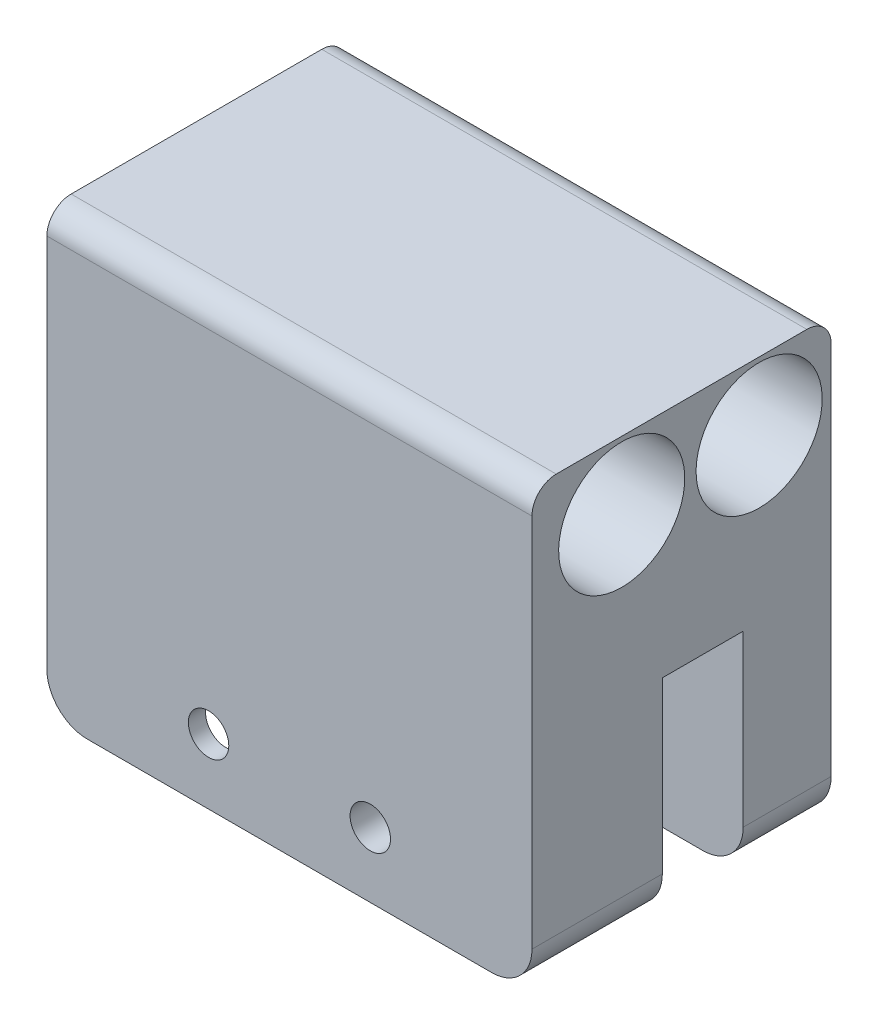
SolidWorks part; units mm, degrees
ref_plane "Front Plane" through (0, 0, 0) normal (0, 0, 1) x (1, 0, 0)
ref_plane "Top Plane" through (0, 0, 0) normal (0, 1, 0) x (1, 0, 0)
ref_plane "Right Plane" through (0, 0, 0) normal (1, 0, 0) x (0, 0, -1)
sketch "Esboço2" plane through (0, 0, 0) normal (0, 0, 1) x (1, 0, 0)
  line L7 (-246.2188, 113.8225) -> (-237.7812, 113.8225)
  line L8 (-201.9668, 113.8225) -> (-194.0332, 113.8225)
  line L9 (-250, 138.1236) -> (-250, 163.2122)
  line L10 (-245, 168.2122) -> (-195, 168.2122)
  line L11 (-190, 163.2122) -> (-190, 138.1236)
  line L21 (-194.0332, 113.8225) -> (-190, 113.8225)
  line L22 (-190, 113.8225) -> (-190, 138.1236)
  line L25 (-250, 138.1236) -> (-250, 113.8225)
  line L26 (-250, 113.8225) -> (-246.2188, 113.8225)
  line L27 (-237.7812, 113.8225) -> (-201.9668, 113.8225)
  arc A5 (-195, 168.2122) -> (-190, 163.2122) centre (-195, 163.2122) cw
  arc A6 (-250, 163.2122) -> (-245, 168.2122) centre (-245, 163.2122) cw
  point P8 (-190, 168.2122)
  point P11 (-250, 168.2122)
  dimension "D1" = 5
extrude "Ressalto-extrusão1" add sketch "Esboço2" along normal up to vertex (40 mm away)
sketch "Esboço4" plane through (-190, 0, 0) normal (1, 0, 0) x (0, 0, -1)
  circle A2 centre (-11.9024, 122.2122) radius 7.8
  circle A3 centre (-11.9024, 122.2122) radius 7.8
  circle A5 centre (-28.9024, 122.2122) radius 7.8
  circle A6 centre (-28.9024, 122.2122) radius 7.8
  dimension "D1" = 0.3
  dimension "D2" = 0.3
extrude "Corte-extrusão1" cut sketch "Esboço4" against normal through all
sketch "Esboço5" plane through (0, 0, 0) normal (0, 0, -1) x (-1, 0, 0)
  line L8 (190, 163.2122) -> (190, 113.8225)
  line L9 (190, 113.8225) -> (250, 113.8225)
  line L10 (250, 113.8225) -> (250, 163.2122)
  line L11 (245, 168.2122) -> (195, 168.2122)
  line L12 (190, 163.2122) -> (190, 113.8225)
  line L13 (190, 113.8225) -> (250, 113.8225)
  line L14 (250, 113.8225) -> (250, 163.2122)
  line L15 (245, 168.2122) -> (195, 168.2122)
  arc A4 (195, 168.2122) -> (190, 163.2122) centre (195, 163.2122) ccw
  arc A5 (250, 163.2122) -> (245, 168.2122) centre (245, 163.2122) ccw
  arc A6 (195, 168.2122) -> (190, 163.2122) centre (195, 163.2122) ccw
  arc A7 (250, 163.2122) -> (245, 168.2122) centre (245, 163.2122) ccw
  dimension "D1" = 0
extrude "Corte-extrusão2" cut sketch "Esboço5" against normal blind 3
sketch "Esboço9" plane through (0, 168.2122, 0) normal (0, 1, 0) x (1, 0, 0)
  line L0 (-220, -40) -> (-220, -3) construction
  line L1 (-195, -40) -> (-245, -40) construction
  line L2 (-245, -3) -> (-195, -3) construction
fillet "Filete2" radius 3 2 edges at (-220, 113.8225, 3) (-220, 113.8225, 40)
sketch "Esboço8" plane through (-250, 0, 0) normal (-1, 0, 0) x (0, 0, 1)
  line L0 (23.8749, 142.2122) -> (23.8749, 152.2122) construction
  line L1 (13.8749, 142.2122) -> (23.8749, 142.2122) construction
  line L2 (13.8749, 142.2122) -> (13.8749, 152.2122) construction
  line L3 (23.8749, 142.2122) -> (23.8749, 152.2122)
  line L4 (13.8749, 142.2122) -> (23.8749, 142.2122)
  line L5 (13.8749, 142.2122) -> (13.8749, 152.2122)
  line L6 (23.8749, 152.2122) -> (23.8749, 182.1915)
  line L7 (23.8749, 182.1915) -> (13.8749, 182.1915)
  line L8 (13.8749, 182.1915) -> (13.8749, 152.2122)
extrude "Corte-extrusão5" cut sketch "Esboço8" against normal through all
sketch "Esboço10" plane through (0, 0, 40) normal (0, 0, 1) x (1, 0, 0)
  line L0 (-715.2149, 160.1731) -> (-165.2149, 160.1731) construction
  line L1 (-190, 116.8225) -> (-190, 163.2122) construction
  line L2 (-250, 163.2122) -> (-250, 116.8225) construction
  circle A0 centre (-210, 160.1731) radius 2.5
  circle A2 centre (-230, 160.1731) radius 2.5
  dimension "D1" = 5
  dimension "D2" = 20
  dimension "D3" = 20
extrude "Corte-extrusão6" cut sketch "Esboço10" against normal through all
sketch "Esboço11" plane through (0, 168.2122, 0) normal (0, 1, 0) x (1, 0, 0)
  line L2 (-190, -13.8749) -> (-190, -3) construction
  line L3 (-245, -3) -> (-195, -3) construction
  line L4 (-220, -40) -> (-220, -3) construction
  line L5 (-195, -40) -> (-245, -40) construction
  circle A0 centre (-199.5, -8.5) radius 4.25
  circle A2 centre (-240.5, -8.5) radius 4.25
  dimension "D1" = 8.5
  dimension "D2" = 9.5
  dimension "D3" = 5.5
extrude "Corte-extrusão7" cut sketch "Esboço11" against normal blind 30
sketch "Esboço12" plane through (-250, 0, 0) normal (-1, 0, 0) x (0, 0, 1)
  line L18 (27.8749, 152.2122) -> (27.8749, 142.2122)
  line L19 (27.8749, 142.2122) -> (37.8749, 142.2122)
  line L20 (37.8749, 142.2122) -> (37.8749, 152.2122)
  line L21 (37.8749, 152.2122) -> (37.8749, 170.6394)
  line L22 (37.8749, 170.6394) -> (27.8749, 170.6394)
  line L23 (27.8749, 170.6394) -> (27.8749, 152.2122)
extrude "Corte-extrusão8" cut sketch "Esboço12" against normal up to vertex (30 mm away) up to point (-220, 168.2122, 40)
mirror "Espelhar1" about plane through (-245, 168.2122, 40) normal (0, -1, 0) of bodies 110 108
delete or keep bodies "Corpo-Excluir/Manter 1" type delete bodies bodies 110
sketch "Esboço13" plane through (-250, 0, 0) normal (-1, 0, 0) x (0, 0, 1)
  line L0 (18.37, 200.6036) -> (18.37, 205.8208) construction
  line L1 (15.07, 205.8208) -> (15.07, 200.6036) construction
  line L2 (18.37, 200.6036) -> (18.37, 205.8208) construction
  line L3 (15.07, 205.8208) -> (15.07, 200.6036) construction
  line L4 (16.72, 205.7122) -> (16.72, 200.7122) construction
  line L5 (15.72, 200.7122) -> (17.72, 200.7122)
  line L6 (15.72, 200.7122) -> (15.72, 205.7122)
  line L7 (15.72, 205.7122) -> (17.72, 205.7122)
  line L8 (17.72, 200.7122) -> (17.72, 205.7122)
  line L9 (15.07, 200.6036) -> (18.37, 200.6036) construction
  line L10 (16.72, 200.6036) -> (16.72, 205.8208) construction
  line L11 (15.3005, 205.8208) -> (18.5545, 205.8208) construction
  point P14 (16.72, 203.2122)
  point P15 (16.72, 203.2122)
  dimension "D1" = 2
  dimension "D2" = 5
extrude "Ressalto-extrusão2" add sketch "Esboço13" along normal blind 5
